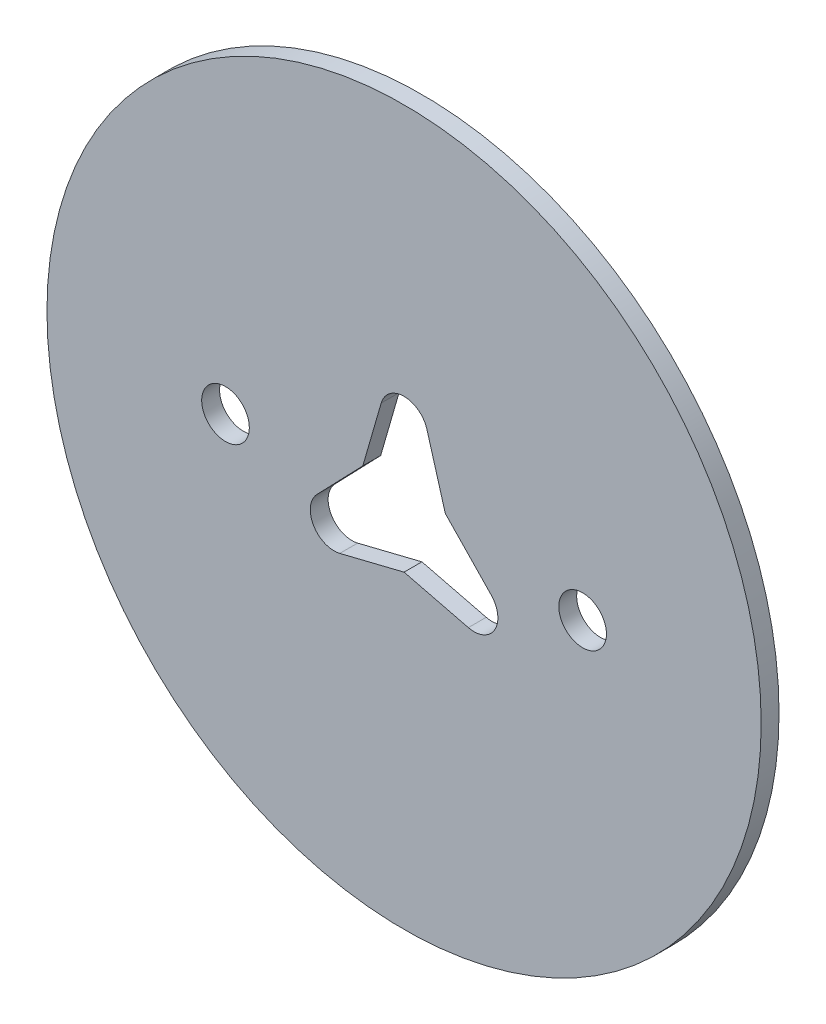
SolidWorks part; units mm, degrees
material "Chrome Stainless Steel"
ref_plane "Front Plane" through (0, 0, 0) normal (0, 0, 1) x (1, 0, 0)
ref_plane "Top Plane" through (0, 0, 0) normal (0, 1, 0) x (1, 0, 0)
ref_plane "Right Plane" through (0, 0, 0) normal (1, 0, 0) x (0, 0, -1)
sketch "Sketch1" plane through (0, 0, 0) normal (0, 0, 1) x (1, 0, 0)
  line L0 (0, 0) -> (30, 0) construction
  line L1 (0, 0) -> (-30, 0) construction
  circle A0 centre (0, 0) radius 30
  circle A1 centre (15, 0) radius 2
  circle A2 centre (-15, 0) radius 2
  dimension "D1" = 60
  dimension "D4" = 4
  dimension "D2" = 15
  dimension "D3" = 15
extrude "Boss-Extrude1" add sketch "Sketch1" along normal blind 1.5
sketch "Sketch2" plane through (0, 0, 0) normal (0, 0, -1) x (-1, 0, 0)
  line L0 (0, 0) -> (0, 14) construction
  line L1 (0, 0) -> (-12.1244, -7) construction
  line L2 (0, 0) -> (12.1244, -7)
  line L3 (-12.1244, -7) -> (-3.4641, 2)
  line L4 (-3.4641, 2) -> (0, 14)
  line L5 (0, 14) -> (3.4641, 2)
  line L6 (0, -4) -> (12.1244, -7)
  line L7 (-12.1244, -7) -> (0, -4)
  line L8 (3.4641, 2) -> (12.1244, -7)
  circle A0 centre (0, 0) radius 14 construction
  circle A1 centre (0, 0) radius 10 construction
  circle A2 centre (0, 0) radius 4 construction
  dimension "D1" = 28
  dimension "D2" = 20
  dimension "D5" = 8
  dimension "D3" = 120
  dimension "D4" = 120
extrude "Cut-Extrude1" cut sketch "Sketch2" against normal blind 10
fillet "Fillet1" radius 2 3 edges at (12.1244, -7, 0.75) (-12.1244, -7, 0.75) (0, 14, 0.75)
equation "\"D3@Sketch1\"=\"D2@Sketch1\""
